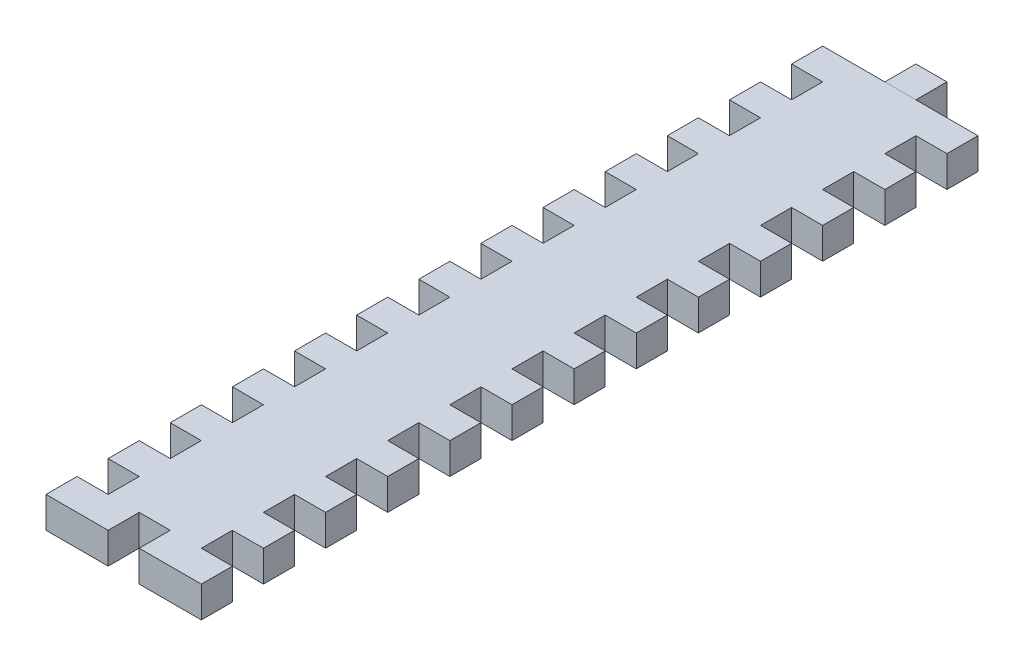
SolidWorks part; units mm, degrees
material "Cedar"
ref_plane "Front Plane" through (0, 0, 0) normal (0, 0, 1) x (1, 0, 0)
ref_plane "Top Plane" through (0, 0, 0) normal (0, 1, 0) x (1, 0, 0)
ref_plane "Right Plane" through (0, 0, 0) normal (1, 0, 0) x (0, 0, -1)
sketch "Sketch1" plane through (0, 0, 0) normal (0, 1, 0) x (1, 0, 0)
  line L0 (0, 30.1667) -> (-4, 30.1667)
  line L1 (-4, 30.1667) -> (-4, 26.1667)
  line L2 (-4, 26.1667) -> (0, 26.1667)
  line L3 (0, 26.1667) -> (0, 22.1667)
  line L4 (16, 30.1667) -> (12, 30.1667)
  line L5 (16, 30.1667) -> (16, 26.1667)
  line L6 (16, 26.1667) -> (12, 26.1667)
  line L7 (12, 26.1667) -> (12, 22.1667)
  line L8 (12, 30.1667) -> (0, 30.1667)
  line L9 (0, 22.1667) -> (-4, 22.1667)
  line L10 (-4, 22.1667) -> (-4, 18.1667)
  line L11 (-4, 18.1667) -> (0, 18.1667)
  line L12 (0, 18.1667) -> (0, 14.1667)
  line L13 (12, 18.1667) -> (12, 14.1667)
  line L14 (16, 22.1667) -> (12, 22.1667)
  line L15 (16, 22.1667) -> (16, 18.1667)
  line L16 (16, 18.1667) -> (12, 18.1667)
  line L17 (0, 14.1667) -> (-4, 14.1667)
  line L18 (-4, 14.1667) -> (-4, 10.1667)
  line L19 (-4, 10.1667) -> (0, 10.1667)
  line L20 (0, 10.1667) -> (0, 6.1667)
  line L21 (12, 10.1667) -> (12, 6.1667)
  line L22 (16, 14.1667) -> (12, 14.1667)
  line L23 (16, 14.1667) -> (16, 10.1667)
  line L24 (16, 10.1667) -> (12, 10.1667)
  line L25 (0, 6.1667) -> (-4, 6.1667)
  line L26 (-4, 6.1667) -> (-4, 2.1667)
  line L27 (-4, 2.1667) -> (0, 2.1667)
  line L28 (0, 2.1667) -> (0, -1.8333)
  line L29 (12, 2.1667) -> (12, -1.8333)
  line L30 (16, 6.1667) -> (12, 6.1667)
  line L31 (16, 6.1667) -> (16, 2.1667)
  line L32 (16, 2.1667) -> (12, 2.1667)
  line L33 (0, -1.8333) -> (-4, -1.8333)
  line L34 (-4, -1.8333) -> (-4, -5.8333)
  line L35 (-4, -5.8333) -> (0, -5.8333)
  line L36 (0, -5.8333) -> (0, -9.8333)
  line L37 (12, -5.8333) -> (12, -9.8333)
  line L38 (16, -1.8333) -> (12, -1.8333)
  line L39 (16, -1.8333) -> (16, -5.8333)
  line L40 (16, -5.8333) -> (12, -5.8333)
  line L41 (0, -9.8333) -> (-4, -9.8333)
  line L42 (-4, -9.8333) -> (-4, -13.8333)
  line L43 (-4, -13.8333) -> (0, -13.8333)
  line L44 (0, -13.8333) -> (0, -17.8333)
  line L45 (12, -13.8333) -> (12, -17.8333)
  line L46 (16, -9.8333) -> (12, -9.8333)
  line L47 (16, -9.8333) -> (16, -13.8333)
  line L48 (16, -13.8333) -> (12, -13.8333)
  line L49 (0, -17.8333) -> (-4, -17.8333)
  line L50 (-4, -17.8333) -> (-4, -21.8333)
  line L51 (-4, -21.8333) -> (0, -21.8333)
  line L52 (0, -21.8333) -> (0, -25.8333)
  line L53 (12, -21.8333) -> (12, -25.8333)
  line L54 (16, -17.8333) -> (12, -17.8333)
  line L55 (16, -17.8333) -> (16, -21.8333)
  line L56 (16, -21.8333) -> (12, -21.8333)
  line L57 (0, -25.8333) -> (-4, -25.8333)
  line L58 (-4, -25.8333) -> (-4, -29.8333)
  line L59 (-4, -29.8333) -> (0, -29.8333)
  line L60 (0, -29.8333) -> (0, -33.8333)
  line L61 (12, -29.8333) -> (12, -33.8333)
  line L62 (16, -25.8333) -> (12, -25.8333)
  line L63 (16, -25.8333) -> (16, -29.8333)
  line L64 (16, -29.8333) -> (12, -29.8333)
  line L65 (0, -33.8333) -> (-4, -33.8333)
  line L66 (-4, -33.8333) -> (-4, -37.8333)
  line L67 (-4, -37.8333) -> (0, -37.8333)
  line L68 (0, -37.8333) -> (0, -41.8333)
  line L69 (12, -37.8333) -> (12, -41.8333)
  line L70 (16, -33.8333) -> (12, -33.8333)
  line L71 (16, -33.8333) -> (16, -37.8333)
  line L72 (16, -37.8333) -> (12, -37.8333)
  line L73 (0, -41.8333) -> (-4, -41.8333)
  line L74 (-4, -41.8333) -> (-4, -45.8333)
  line L75 (-4, -45.8333) -> (0, -45.8333)
  line L76 (0, -45.8333) -> (0, -49.8333)
  line L77 (12, -45.8333) -> (12, -49.8333)
  line L78 (16, -41.8333) -> (12, -41.8333)
  line L79 (16, -41.8333) -> (16, -45.8333)
  line L80 (16, -45.8333) -> (12, -45.8333)
  line L81 (0, -49.8333) -> (-4, -49.8333)
  line L82 (-4, -49.8333) -> (-4, -53.8333)
  line L83 (-4, -53.8333) -> (0, -53.8333)
  line L84 (0, -53.8333) -> (0, -57.8333)
  line L85 (12, -53.8333) -> (12, -57.8333)
  line L86 (16, -49.8333) -> (12, -49.8333)
  line L87 (16, -49.8333) -> (16, -53.8333)
  line L88 (16, -53.8333) -> (12, -53.8333)
  line L89 (0, -57.8333) -> (-4, -57.8333)
  line L90 (-4, -57.8333) -> (-4, -61.8333)
  line L91 (-4, -61.8333) -> (0, -61.8333)
  line L92 (0, -61.8333) -> (0, -65.8333)
  line L93 (12, -61.8333) -> (12, -65.8333)
  line L94 (16, -57.8333) -> (12, -57.8333)
  line L95 (16, -57.8333) -> (16, -61.8333)
  line L96 (16, -61.8333) -> (12, -61.8333)
  line L97 (0, -65.8333) -> (-4, -65.8333)
  line L98 (-4, -65.8333) -> (-4, -69.8333)
  line L102 (16, -65.8333) -> (12, -65.8333)
  line L103 (16, -65.8333) -> (16, -69.8333)
  line L104 (16, -69.8333) -> (-4, -69.8333)
  dimension "D1" = 4
  dimension "D2" = 4
  dimension "D3" = 4
  dimension "D4" = 4
  dimension "D5" = 12
  dimension "D6" = 4
extrude "Boss-Extrude1" add sketch "Sketch1" along normal blind 4
sketch "Sketch2" plane through (0, 4, 0) normal (0, 1, 0) x (1, 0, 0)
  line L0 (16, 30.1667) -> (-4, 30.1667) construction
  line L1 (4, 34.1667) -> (8, 34.1667)
  line L2 (4, 34.1667) -> (4, 30.1667)
  line L3 (4, 30.1667) -> (8, 30.1667)
  line L4 (8, 34.1667) -> (8, 30.1667)
  line L7 (0, 26.1667) -> (12, 26.1667) construction
  line L8 (6, 26.1667) -> (6, 37.3774) construction
  dimension "D1" = 4
  dimension "D2" = 2
  dimension "D3" = 2
extrude "Boss-Extrude2" add sketch "Sketch2" against normal blind 4 separate body
sketch "Sketch3" plane through (0, 4, 0) normal (0, 1, 0) x (1, 0, 0)
  line L0 (-4, -69.8333) -> (16, -69.8333) construction
  line L1 (4, -69.8333) -> (8, -69.8333)
  line L2 (4, -69.8333) -> (4, -65.8333)
  line L3 (4, -65.8333) -> (8, -65.8333)
  line L4 (8, -69.8333) -> (8, -65.8333)
  line L5 (6, 34.1667) -> (6, -69.8333) construction
  line L6 (8, 34.1667) -> (4, 34.1667) construction
  dimension "D1" = 4
  dimension "D2" = 4
extrude "Cut-Extrude1" cut sketch "Sketch3" against normal blind 10
